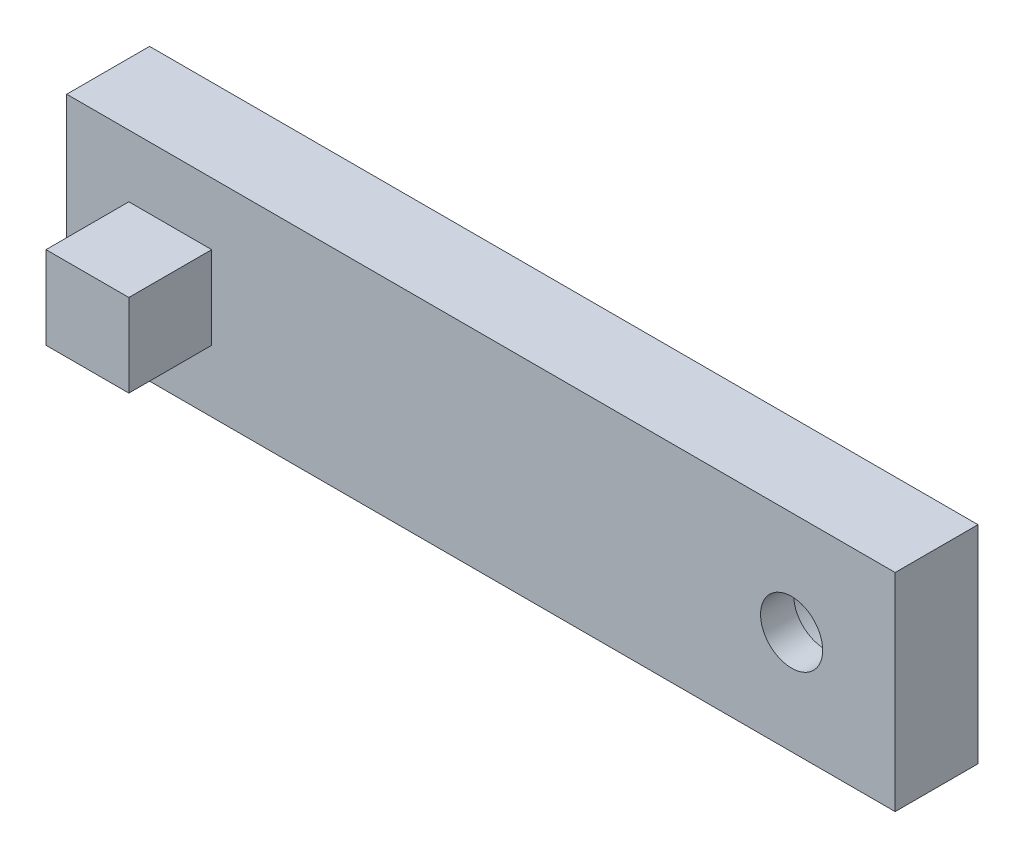
SolidWorks part; units mm, degrees
ref_plane "Plan de face" through (0, 0, 0) normal (0, 0, 1) x (1, 0, 0)
ref_plane "Plan de dessus" through (0, 0, 0) normal (0, 1, 0) x (1, 0, 0)
ref_plane "Plan de droite" through (0, 0, 0) normal (1, 0, 0) x (0, 0, -1)
sketch "Esquisse1" plane through (0, 0, 0) normal (0, 0, 1) x (1, 0, 0)
  line L1 (100, 25) -> (-100, 25)
  line L2 (100, 25) -> (100, -25)
  line L3 (100, -25) -> (-100, -25)
  line L4 (-100, 25) -> (-100, -25)
  line L5 (100, 25) -> (-100, -25) construction
  line L6 (100, -25) -> (-100, 25) construction
  point P0 (0, 0)
  dimension "D1" = 200
  dimension "D2" = 50
extrude "Boss.-Extru.1" add sketch "Esquisse1" along normal blind 20
sketch "Esquisse2" plane through (0, 0, 20) normal (0, 0, 1) x (1, 0, 0)
  line L0 (-100, -25) -> (100, -25) construction
  line L1 (-65, 10) -> (-85, 10)
  line L2 (-65, 10) -> (-65, -10)
  line L3 (-65, -10) -> (-85, -10)
  line L4 (-85, 10) -> (-85, -10)
  line L5 (-65, 10) -> (-85, -10) construction
  line L6 (-65, -10) -> (-85, 10) construction
  line L7 (-100, 25) -> (-100, -25) construction
  point P0 (-75, 0)
  dimension "D1" = 20
  dimension "D2" = 20
  dimension "D3" = 15
  dimension "D4" = 15
extrude "Boss.-Extru.2" add sketch "Esquisse2" along normal blind 20
sketch "Esquisse3" plane through (0, 0, 20) normal (0, 0, 1) x (1, 0, 0)
  line L0 (100, -25) -> (100, 25) construction
  line L1 (100, 25) -> (-100, 25) construction
  circle A0 centre (75, 0) radius 7.5
  dimension "D1" = 15
  dimension "D2" = 25
  dimension "D3" = 25
extrude "Enlèv. mat.-Extru.1" cut sketch "Esquisse3" against normal blind 20
sketch "Esquisse8" plane through (0, 0, 0) normal (0, 0, -1) x (-1, 0, 0)
  circle A0 centre (-75, 0) radius 16.25
  dimension "D1" = 32.5
extrude "Enlèv. mat.-Extru.3" cut sketch "Esquisse8" against normal blind 12
